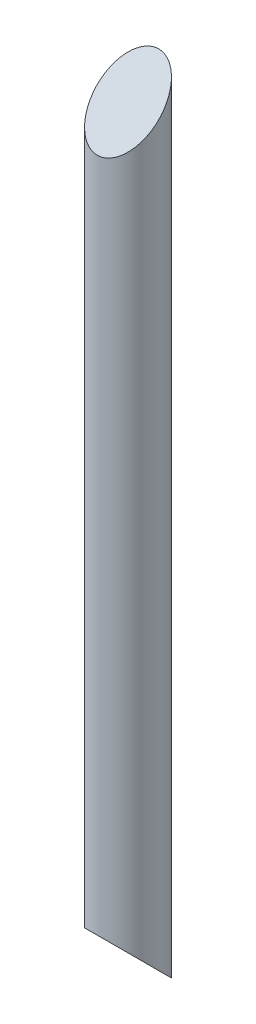
SolidWorks part; units mm, degrees
ref_plane "Front Plane" through (0, 0, 0) normal (0, 0, 1) x (1, 0, 0)
ref_plane "Top Plane" through (0, 0, 0) normal (0, 1, 0) x (1, 0, 0)
ref_plane "Right Plane" through (0, 0, 0) normal (1, 0, 0) x (0, 0, -1)
sketch "Sketch1" plane through (0, 0, 0) normal (0, 1, 0) x (1, 0, 0)
  circle A0 centre (0, 0) radius 31.75
  dimension "D1" = 63.5
extrude "Boss-Extrude1" add sketch "Sketch1" along normal blind 698.5
sketch "Sketch2" plane through (0, 698.5, 0) normal (0, 1, 0) x (1, 0, 0)
  circle A0 centre (0, 0) radius 31.75
extrude "Boss-Extrude2" add sketch "Sketch2" along normal blind 63.5
sketch "Sketch3" plane through (0, 0, 0) normal (0, -1, 0) x (1, 0, 0)
  circle A0 centre (0, 0) radius 31.75
extrude "Boss-Extrude3" add sketch "Sketch3" along normal blind 63.5
ref_plane "Plane1" through (31.75, 0, 0) normal (1, 0, 0) x (0, 0, -1)
sketch "Sketch4" plane through (31.75, 0, 0) normal (1, 0, 0) x (0, 0, -1)
  line L0 (0, 698.5) -> (31.75, 698.5)
  line L1 (31.75, 698.5) -> (-31.75, 698.5) construction
  line L2 (31.75, 698.5) -> (31.75, 762)
  line L3 (31.75, 762) -> (-31.75, 762)
  line L4 (-31.75, 762) -> (-31.75, 698.5)
  line L5 (-31.75, 762) -> (-31.75, -63.5) construction
  line L6 (-31.75, 698.5) -> (0, 698.5)
  line L7 (-31.75, 698.5) -> (31.75, 762)
  line L8 (0, 0) -> (31.75, 0)
  line L9 (-31.75, 0) -> (31.75, 0) construction
  line L10 (31.75, 0) -> (31.75, -63.5)
  line L11 (31.75, -63.5) -> (31.75, 762) construction
  line L12 (31.75, -63.5) -> (-31.75, -63.5)
  line L13 (-31.75, -63.5) -> (-31.75, 0)
  line L14 (-31.75, 0) -> (0, 0)
  line L15 (-31.75, 0) -> (31.75, -63.5)
extrude "Cut-Extrude1" cut sketch "Sketch4" against normal blind 63.5 contours L4 L7 L3 | L15 L13 L12
equation "\"LengthOfSideNoodle\"= \"Length Desired@Drivetrain.SLDASM\" + 1.5"
equation "\"D1@Boss-Extrude1\"=\"LengthOfSideNoodle\""
